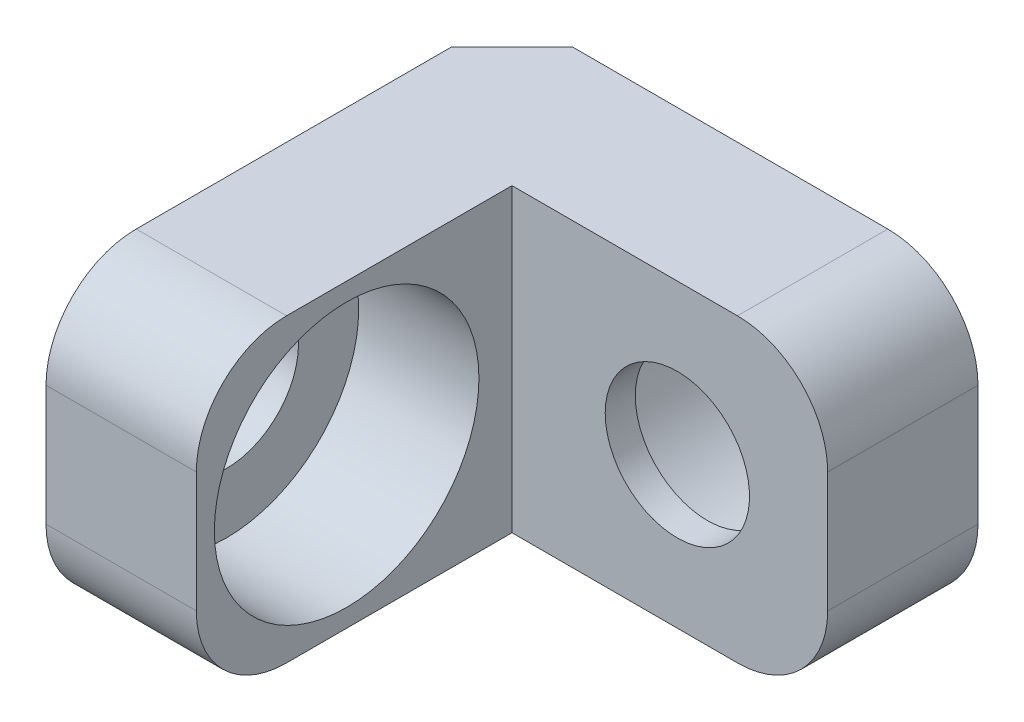
SolidWorks part; units mm, degrees
ref_plane "Front Plane" through (0, 0, 0) normal (0, 0, 1) x (1, 0, 0)
ref_plane "Top Plane" through (0, 0, 0) normal (0, 1, 0) x (1, 0, 0)
ref_plane "Right Plane" through (0, 0, 0) normal (1, 0, 0) x (0, 0, -1)
sketch "Sketch1" plane through (0, 0, 0) normal (0, 1, 0) x (1, 0, 0)
  line L0 (0, 0) -> (0, 7.75)
  line L1 (0, 7.75) -> (7.75, 7.75)
  line L2 (7.75, 7.75) -> (7.75, 5.25)
  line L3 (7.75, 5.25) -> (2.5, 5.25)
  line L4 (2.5, 5.25) -> (2.5, 0)
  line L5 (2.5, 0) -> (0, 0)
  dimension "D1" = 2.5
  dimension "D2" = 7.75
extrude "Boss-Extrude2" add sketch "Sketch1" along normal blind 5
chamfer "Chamfer1" distance 1 angle 45 1 edges at (0, 2.5, -7.75)
hole_wizard "CBORE for M2 SHCS1" positions "Sketch3" profile "Sketch2" counterbore size "M2" standard "ANSI Metric" end condition through all
sketch "Sketch3" plane through (0, 0, -7.75) normal (0, 0, -1) x (-1, 0, 0)
  line L0 (-7.75, 5) -> (-7.75, 0) construction
  line L2 (-7.75, 0) -> (-1, 0) construction
  point P0 (-5.25, 2.5)
  point P7 (-2.6427, 0)
  dimension "D1" = 2.5
  dimension "D2" = 2.5
sketch "Sketch2" plane through (5.25, 2.5, -7.75) normal (1, 0, 0) x (0, 1, 0)
  line L0 (0, 0) -> (0, 7.75)
  line L1 (0, 7.75) -> (1.2, 7.75)
  line L3 (1.2, 7.75) -> (1.2, 2)
  line L4 (1.2, 2) -> (2.2, 2)
  line L5 (2.2, 2) -> (2.2, 0)
  line L7 (2.2, 0) -> (0, 0)
  line L11 (0, -6.35) -> (0, 107.95) construction
  dimension "Thru Hole Dia." = 2.4
  dimension "Thru Hole Depth" = 7.75
  dimension "C'Bore Dia." = 4.4
  dimension "C'Bore Depth" = 2
fillet "Fillet2" radius 1.5 4 edges at (1.25, 0, 0) (1.25, 5, 0) (7.75, 0, -6.5) (7.75, 5, -6.5)
hole_wizard "CBORE for M2 SHCS3" positions "Sketch7" profile "Sketch6" counterbore size "M2" standard "ANSI Metric" end condition through all
sketch "Sketch7" plane through (2.5, 0, 0) normal (1, 0, 0) x (0, 0, -1)
  line L0 (0, 3.5) -> (0, 1.5) construction
  line L1 (1.5, 5) -> (5.25, 5) construction
  point P0 (2.5, 2.5)
  dimension "D1" = 2.5
  dimension "D2" = 2.5
sketch "Sketch6" plane through (2.5, 2.5, -2.5) normal (0, 1, 0) x (0, 0, -1)
  line L0 (0, 0) -> (0, 2.5)
  line L1 (0, 2.5) -> (1.2, 2.5)
  line L3 (1.2, 2.5) -> (1.2, 2)
  line L4 (1.2, 2) -> (2.2, 2)
  line L5 (2.2, 2) -> (2.2, 0)
  line L7 (2.2, 0) -> (0, 0)
  line L11 (0, -6.35) -> (0, 107.95) construction
  dimension "Thru Hole Dia." = 2.4
  dimension "Thru Hole Depth" = 2.5
  dimension "C'Bore Dia." = 4.4
  dimension "C'Bore Depth" = 2
